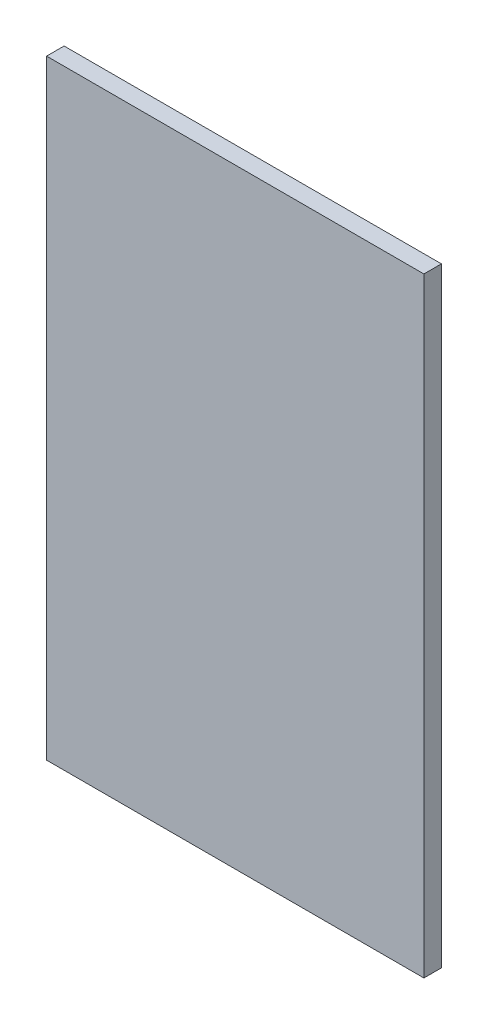
SolidWorks part; units mm, degrees
ref_plane "Front Plane" through (0, 0, 0) normal (0, 0, 1) x (1, 0, 0)
ref_plane "Top Plane" through (0, 0, 0) normal (0, 1, 0) x (1, 0, 0)
ref_plane "Right Plane" through (0, 0, 0) normal (1, 0, 0) x (0, 0, -1)
sketch "Sketch1" plane through (0, 0, 0) normal (0, 0, 1) x (1, 0, 0)
  line L1 (194, -313.5) -> (-194, -313.5)
  line L2 (194, -313.5) -> (194, 313.5)
  line L3 (194, 313.5) -> (-194, 313.5)
  line L4 (-194, -313.5) -> (-194, 313.5)
  line L5 (194, -313.5) -> (-194, 313.5) construction
  line L6 (194, 313.5) -> (-194, -313.5) construction
  point P0 (0, 0)
  dimension "D1" = 627
  dimension "D2" = 388
extrude "Boss-Extrude1" add sketch "Sketch1" along normal blind 18
equation "\"H_DSP\"=18"
equation "\"D1@Boss-Extrude1\"=\"H_DSP\""
